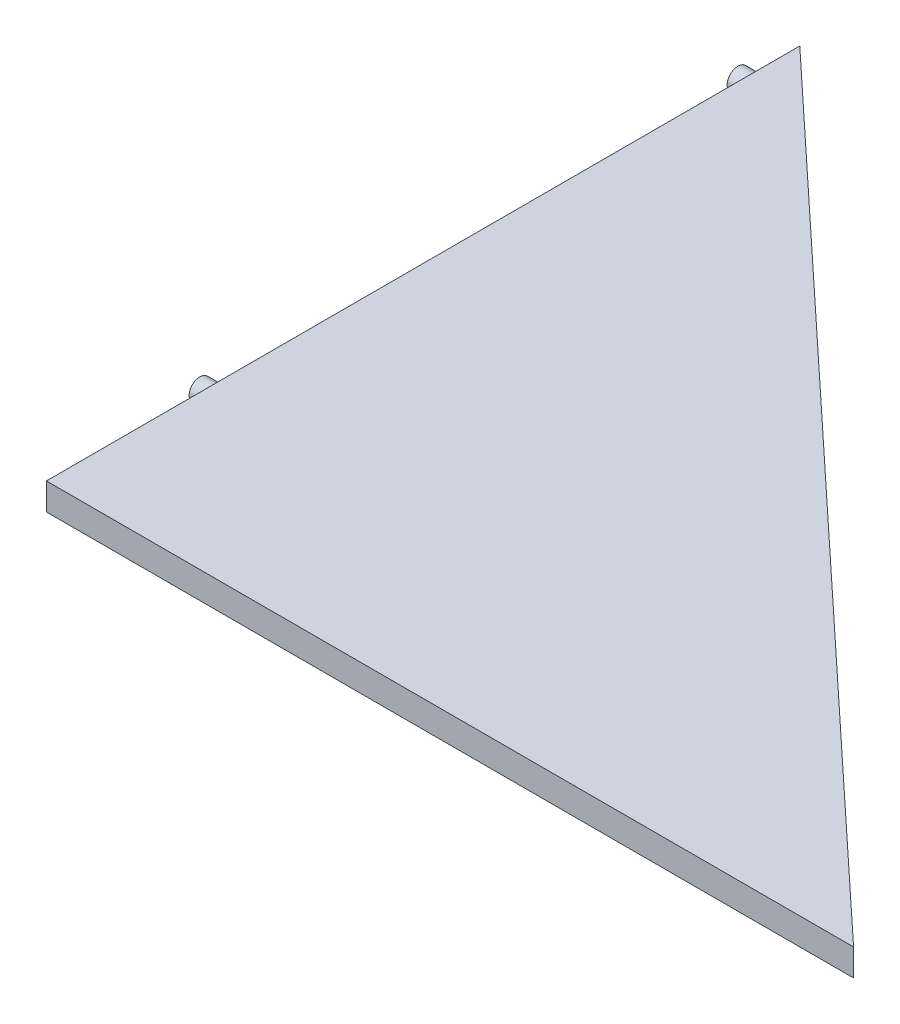
SolidWorks part; units mm, degrees
ref_plane "Front Plane" through (0, 0, 0) normal (0, 0, 1) x (1, 0, 0)
ref_plane "Top Plane" through (0, 0, 0) normal (0, 1, 0) x (1, 0, 0)
ref_plane "Right Plane" through (0, 0, 0) normal (1, 0, 0) x (0, 0, -1)
sketch "Sketch1" plane through (0, 0, 0) normal (0, 1, 0) x (1, 0, 0)
  line L0 (-50.2638, 46.9129) -> (99.7362, -93.0871)
  line L1 (-50.2638, -93.0871) -> (99.7362, -93.0871)
  line L2 (-50.2638, -93.0871) -> (-50.2638, 46.9129)
  line L5 (-50.2638, -93.0871) -> (0, 0) construction
  line L6 (-50.2638, 46.9129) -> (99.7362, -93.0871) construction
  point P0 (0, 0)
  dimension "D1" = 150
  dimension "D2" = 140
extrude "Boss-Extrude1" add sketch "Sketch1" along normal blind 5
sketch "Sketch2" plane through (-50.2638, 0, 0) normal (-1, 0, 0) x (0, 0, 1)
  line L0 (-46.9129, 5) -> (93.0871, 5) construction
  line L1 (-46.9129, 0) -> (93.0871, 0) construction
  circle A0 centre (-38.4214, 2.5) radius 2
  circle A1 centre (61.5786, 2.5) radius 2
  dimension "D3" = 4
  dimension "D4" = 4
  dimension "D1" = 100
  dimension "D2" = 2.5
  dimension "D5" = 2.5
extrude "Boss-Extrude2" add sketch "Sketch2" along normal blind 3
